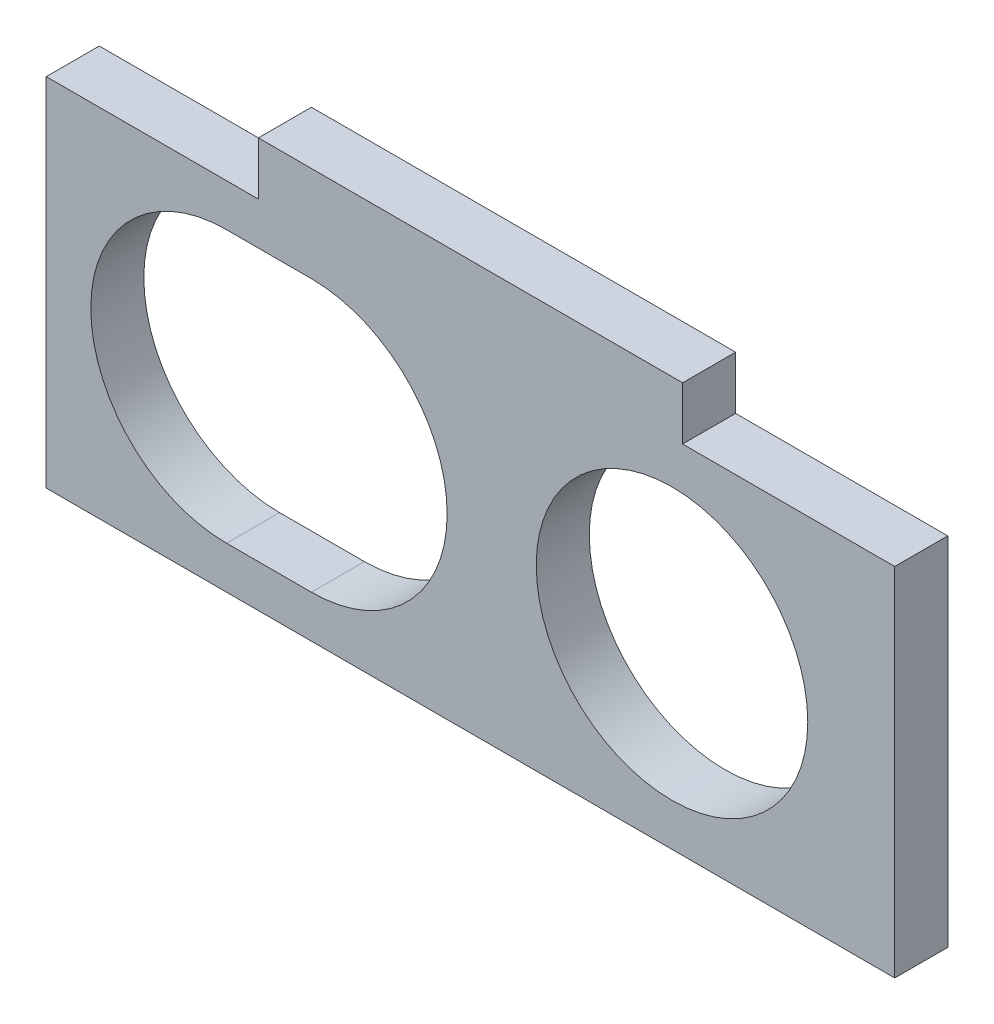
SolidWorks part; units mm, degrees
ref_plane "Front Plane" through (0, 0, 0) normal (0, 0, 1) x (1, 0, 0)
ref_plane "Top Plane" through (0, 0, 0) normal (0, 1, 0) x (1, 0, 0)
ref_plane "Right Plane" through (0, 0, 0) normal (1, 0, 0) x (0, 0, -1)
sketch "Sketch1" plane through (0, 0, 0) normal (0, 0, 1) x (1, 0, 0)
  line L1 (-25.4, -12.2555) -> (25.4, -12.2555)
  line L2 (-25.4, -12.2555) -> (-25.4, 12.2555)
  line L3 (-25.4, 12.2555) -> (25.4, 12.2555)
  line L4 (25.4, -12.2555) -> (25.4, 12.2555)
  line L5 (-25.4, -12.2555) -> (25.4, 12.2555) construction
  line L6 (-25.4, 12.2555) -> (25.4, -12.2555) construction
  point P0 (0, 0)
  dimension "D1" = 50.8
  dimension "D2" = 24.511
extrude "Boss-Extrude1" add sketch "Sketch1" along normal blind 3.175
sketch "Sketch2" plane through (0, 0, 3.175) normal (0, 0, 1) x (1, 0, 0)
  line L0 (-12.065, 6.5405) -> (12.065, 6.5405) construction
  line L1 (-25.4, 12.2555) -> (-12.7, 12.2555)
  line L2 (-25.4, 12.2555) -> (-25.4, 9.0805)
  line L3 (-25.4, 9.0805) -> (-12.7, 9.0805)
  line L4 (-12.7, 12.2555) -> (-12.7, 9.0805)
  line L5 (25.4, 12.2555) -> (12.7, 12.2555)
  line L6 (25.4, 12.2555) -> (25.4, 9.0805)
  line L7 (25.4, 9.0805) -> (12.7, 9.0805)
  line L8 (12.7, 12.2555) -> (12.7, 9.0805)
  line L9 (12.065, -1.5875) -> (-12.065, -1.5875) construction
  line L10 (-25.4, 9.0805) -> (25.4, 9.0805) construction
  line L11 (0, 9.0805) -> (0, -12.2555) construction
  line L12 (-25.4, -12.2555) -> (25.4, -12.2555) construction
  line L13 (-14.605, -1.5875) -> (-9.525, -1.5875) construction
  line L14 (-14.605, -9.7155) -> (-14.605, 6.5405) construction
  line L15 (-9.525, -9.7155) -> (-9.525, 6.5405) construction
  line L16 (-14.605, 6.5405) -> (-9.525, 6.5405)
  line L17 (-14.605, -9.7155) -> (-9.525, -9.7155)
  arc A0 (-14.605, 6.5405) -> (-14.605, -9.7155) centre (-14.605, -1.5875) ccw
  circle A1 centre (12.065, -1.5875) radius 8.128
  arc A2 (-9.525, 6.5405) -> (-9.525, -9.7155) centre (-9.525, -1.5875) cw
  point P20 (0, -1.5875)
  point P21 (0, -1.5875)
  point P24 (-12.065, -1.5875)
  point P27 (-14.605, -1.5875)
  point P30 (-9.525, -1.5875)
  point P31 (0, 0)
  point P32 (0, 0)
  dimension "D4" = 16.256
  dimension "D1" = 12.7
  dimension "D2" = 12.7
  dimension "D3" = 3.175
  dimension "D5" = 24.13
  dimension "D6" = 5.08
extrude "Cut-Extrude1" cut sketch "Sketch2" against normal blind 3.175
